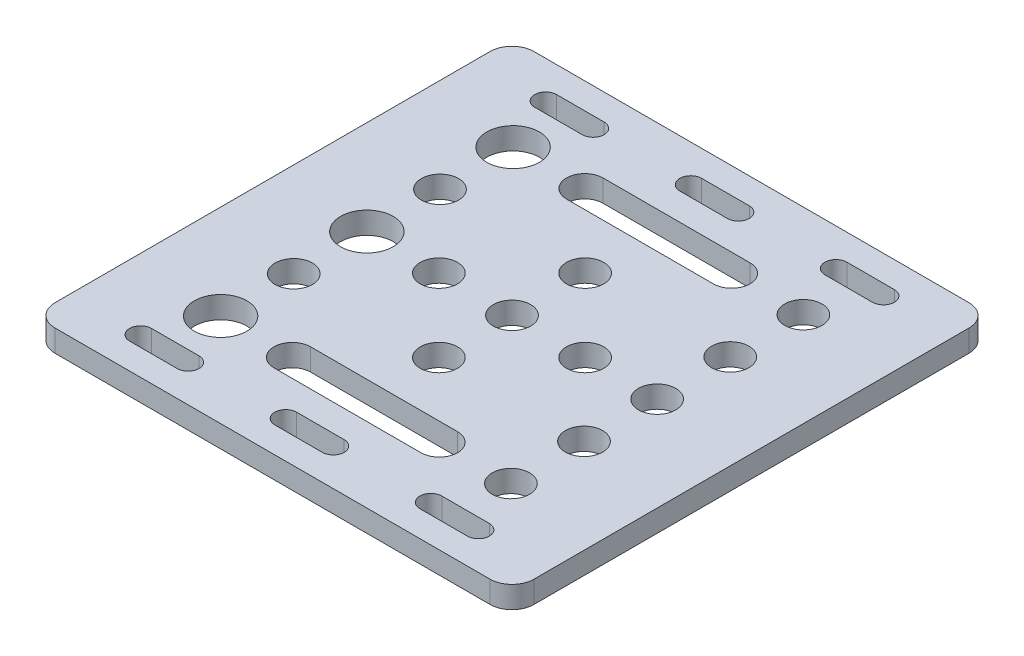
SolidWorks part; units mm, degrees
material "3003 Alloy"
ref_plane "Front Plane" through (0, 0, 0) normal (0, 0, 1) x (1, 0, 0)
ref_plane "Top Plane" through (0, 0, 0) normal (0, 1, 0) x (1, 0, 0)
ref_plane "Right Plane" through (0, 0, 0) normal (1, 0, 0) x (0, 0, -1)
sketch "Sketch1" plane through (0, 0, 0) normal (0, 1, 0) x (1, 0, 0)
  line L1 (-32.75, -32.75) -> (32.75, -32.75)
  line L2 (-32.75, -32.75) -> (-32.75, 32.75)
  line L3 (-32.75, 32.75) -> (32.75, 32.75)
  line L4 (32.75, -32.75) -> (32.75, 32.75)
  line L5 (-32.75, -32.75) -> (32.75, 32.75) construction
  line L6 (-32.75, 32.75) -> (32.75, -32.75) construction
  point P0 (0, 0)
  dimension "D1" = 65.5
extrude "Boss-Extrude1" add sketch "Sketch1" along normal blind 3
sketch "Sketch5" plane through (0, 0, 0) normal (0, 1, 0) x (1, 0, 0)
  line L1 (-32.75, 32.75) -> (-32.75, -32.75) construction
  line L2 (32.75, 32.75) -> (-32.75, 32.75) construction
  circle A1 centre (-19.85, 20) radius 2.55
  dimension "D2" = 5.1
  dimension "D4" = 12.75
  dimension "D5" = 12.9
extrude "Cut-Extrude5" cut sketch "Sketch5" along normal through all
pattern_linear "LPattern2" count 5 spacing 10 along (0, 0, 1) count 2 spacing 39.7 along (1, 0, 0) of "Cut-Extrude5"
sketch "Sketch7" plane through (0, 0, 0) normal (0, 1, 0) x (1, 0, 0)
  circle A0 centre (0, 0) radius 2.55
  circle A1 centre (-19.85, 20) radius 2.55 construction
extrude "Cut-Extrude6" cut sketch "Sketch7" along normal through all
sketch "Sketch8" plane through (0, 0, 0) normal (0, 1, 0) x (1, 0, 0)
  circle A0 centre (0, 10) radius 2.55
  circle A1 centre (0, 0) radius 2.55 construction
  dimension "D1" = 10
extrude "Cut-Extrude7" cut sketch "Sketch8" along normal through all
pattern_circular "CirPattern1" count 4 every 90 about axis through (0, 0, 0) along (0, 1, 0) of "Cut-Extrude7"
sketch "Sketch3" plane through (0, 0, 0) normal (0, 1, 0) x (1, 0, 0)
  line L0 (-32.75, 32.75) -> (-32.75, -32.75) construction
  line L1 (32.75, 32.75) -> (-32.75, 32.75) construction
  circle A0 centre (-19.85, 20) radius 3.6
  dimension "D1" = 7.2
  dimension "D2" = 12.9
  dimension "D3" = 12.75
extrude "Cut-Extrude4" cut sketch "Sketch3" against normal through all and the other way through all
pattern_linear "LPattern1" count 3 spacing 20 along (0, 0, 1) of "Cut-Extrude4"
sketch "Sketch9" plane through (0, 0, 0) normal (0, 1, 0) x (1, 0, 0)
  line L0 (-23.1, 27.7) -> (-16.6, 27.7) construction
  line L1 (-23.1, 29.2) -> (-16.6, 29.2)
  line L2 (-23.1, 26.2) -> (-16.6, 26.2)
  line L3 (32.75, 32.75) -> (-32.75, 32.75) construction
  line L4 (-32.75, 32.75) -> (-32.75, -32.75) construction
  arc A0 (-23.1, 29.2) -> (-23.1, 26.2) centre (-23.1, 27.7) ccw
  arc A1 (-16.6, 26.2) -> (-16.6, 29.2) centre (-16.6, 27.7) ccw
  point P2 (-19.85, 27.7)
  dimension "D3" = 1.5
  dimension "D1" = 5.05
  dimension "D2" = 12.9
  dimension "D4" = 6.5
extrude "Cut-Extrude8" cut sketch "Sketch9" along normal through all
pattern_linear "LPattern3" count 3 spacing 19.85 along (1, 0, 0) count 2 spacing 55.4 along (0, 0, 1) of "Cut-Extrude8"
sketch "Sketch10" plane through (0, 0, 0) normal (0, 1, 0) x (1, 0, 0)
  line L0 (-10.05, 20) -> (10.05, 20) construction
  line L1 (-10.05, 22.5) -> (10.05, 22.5)
  line L2 (-10.05, 17.5) -> (10.05, 17.5)
  line L3 (32.75, 32.75) -> (-32.75, 32.75) construction
  arc A0 (-10.05, 22.5) -> (-10.05, 17.5) centre (-10.05, 20) ccw
  arc A1 (10.05, 17.5) -> (10.05, 22.5) centre (10.05, 20) ccw
  point P2 (0, 20)
  dimension "D1" = 2.5
  dimension "D2" = 12.75
  dimension "D3" = 20.1
extrude "Cut-Extrude9" cut sketch "Sketch10" along normal through all
pattern_linear "LPattern4" count 2 spacing 40 along (0, 0, 1) of "Cut-Extrude9"
fillet "Fillet1" radius 3 4 edges at (32.75, 1.5, 32.75) (32.75, 1.5, -32.75) (-32.75, 1.5, 32.75) (-32.75, 1.5, -32.75)
